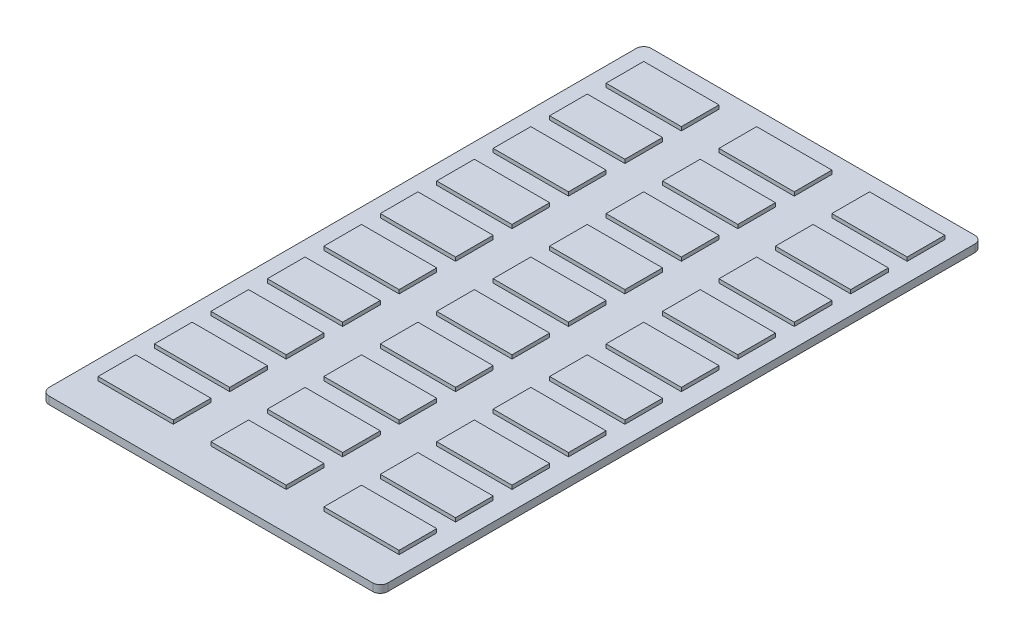
SolidWorks part; units mm, degrees
ref_plane "Front Plane" through (0, 0, 0) normal (0, 0, 1) x (1, 0, 0)
ref_plane "Top Plane" through (0, 0, 0) normal (0, 1, 0) x (1, 0, 0)
ref_plane "Right Plane" through (0, 0, 0) normal (1, 0, 0) x (0, 0, -1)
sketch "Sketch1" plane through (0, 0, 0) normal (0, 1, 0) x (1, 0, 0)
  line L1 (45, -80) -> (-45, -80)
  line L2 (45, -80) -> (45, 80)
  line L3 (45, 80) -> (-45, 80)
  line L4 (-45, -80) -> (-45, 80)
  line L5 (45, -80) -> (-45, 80) construction
  line L6 (45, 80) -> (-45, -80) construction
  point P0 (0, 0)
  dimension "D1" = 90
  dimension "D2" = 160
extrude "Boss-Extrude1" add sketch "Sketch1" along normal blind 2
sketch "Sketch2" plane through (0, 2, 0) normal (0, 1, 0) x (1, 0, 0)
  line L0 (-45, 80) -> (-45, -80) construction
  line L1 (-40, 75) -> (-20, 75)
  line L2 (-40, 75) -> (-40, 65)
  line L3 (-40, 65) -> (-20, 65)
  line L4 (-20, 75) -> (-20, 65)
  line L5 (45, 80) -> (-45, 80) construction
  line L6 (-40, 60) -> (-40, 50)
  line L7 (-20, 60) -> (-20, 50)
  line L8 (-40, 60) -> (-20, 60)
  line L9 (-40, 45) -> (-40, 35)
  line L10 (-20, 45) -> (-20, 35)
  line L11 (-40, 45) -> (-20, 45)
  line L12 (-40, 30) -> (-40, 20)
  line L13 (-20, 30) -> (-20, 20)
  line L14 (-40, 30) -> (-20, 30)
  line L15 (-40, 15) -> (-40, 5)
  line L16 (-20, 15) -> (-20, 5)
  line L17 (-40, 15) -> (-20, 15)
  line L18 (-40, 0) -> (-40, -10)
  line L19 (-20, 0) -> (-20, -10)
  line L20 (-40, 0) -> (-20, 0)
  line L21 (-40, -15) -> (-40, -25)
  line L22 (-20, -15) -> (-20, -25)
  line L23 (-40, -15) -> (-20, -15)
  line L24 (-40, -30) -> (-40, -40)
  line L25 (-20, -30) -> (-20, -40)
  line L26 (-40, -30) -> (-20, -30)
  line L27 (-40, -45) -> (-40, -55)
  line L28 (-20, -45) -> (-20, -55)
  line L29 (-40, -45) -> (-20, -45)
  line L30 (-40, -60) -> (-40, -70)
  line L31 (-20, -60) -> (-20, -70)
  line L32 (-40, -60) -> (-20, -60)
  line L33 (-40, 50) -> (-20, 50)
  line L34 (-40, 35) -> (-20, 35)
  line L35 (-40, 20) -> (-20, 20)
  line L36 (-40, 5) -> (-20, 5)
  line L37 (-40, -10) -> (-20, -10)
  line L38 (-40, -25) -> (-20, -25)
  line L39 (-20, -40) -> (-40, -40)
  line L40 (-40, -55) -> (-20, -55)
  line L41 (-40, -70) -> (-20, -70)
  dimension "D1" = 20
  dimension "D2" = 10
  dimension "D3" = 5
  dimension "D4" = 5
  dimension "D5" = 10
extrude "Boss-Extrude2" add sketch "Sketch2" along normal blind 1 contours L41 L31 L32 L30 | L40 L28 L29 L27 | L39 L24 L26 L25 | L38 L22 L23 L21 | L37 L19 L20 L18 | L36 L16 L17 L15 | L35 L13 L14 L12 | L34 L10 L11 L9 | L33 L7 L8 L6 | L2 L1 L4 L3
pattern_linear "LPattern1" count 3 spacing 30 along (1, 0, 0) of "Boss-Extrude2"
fillet "Fillet1" radius 2 4 edges at (45, 1, -80) (45, 1, 80) (-45, 1, 80) (-45, 1, -80)
